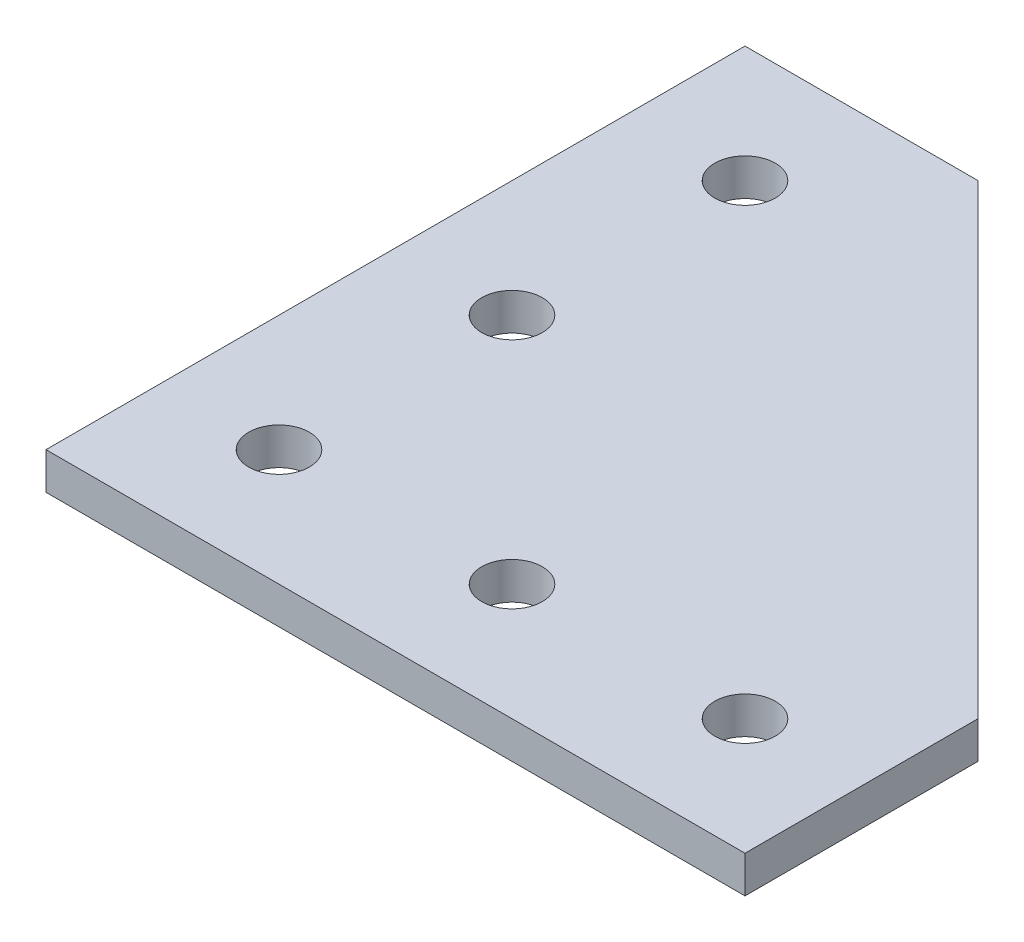
SolidWorks part; units mm, degrees
material "6061-T6 (SS)"
ref_plane "Front Plane" through (0, 0, 0) normal (0, 0, 1) x (1, 0, 0)
ref_plane "Top Plane" through (0, 0, 0) normal (0, 1, 0) x (1, 0, 0)
ref_plane "Right Plane" through (0, 0, 0) normal (1, 0, 0) x (0, 0, -1)
sketch "Sketch1" plane through (0, 0, 0) normal (0, 1, 0) x (1, 0, 0)
  line L0 (60, 0) -> (60, 20)
  line L1 (0, 0) -> (60, 0)
  line L2 (0, 0) -> (0, 60)
  line L3 (0, 60) -> (20, 60)
  line L4 (60, 20) -> (20, 60)
  line L5 (10, 10) -> (50, 10) construction
  line L6 (10, 50) -> (10, 10) construction
  circle A0 centre (50, 10) radius 2.6
  circle A1 centre (10, 50) radius 2.6
  circle A2 centre (30, 10) radius 2.6
  circle A3 centre (10, 10) radius 2.6
  circle A4 centre (10, 30) radius 2.6
  dimension "D5" = 5.2
  dimension "D1" = 60
  dimension "D3" = 20
  dimension "D6" = 40
  dimension "D7" = 10
  dimension "D8" = 10
  dimension "D9" = 40
  dimension "D2" = 60
  dimension "D4" = 20
extrude "Boss-Extrude1" add sketch "Sketch1" along normal blind 3.175
equation "\"D8@Sketch1\"=\"D7@Sketch1\""
equation "\"D9@Sketch1\"=\"D6@Sketch1\""
equation "\"D2@Sketch1\"=\"D1@Sketch1\""
equation "\"D4@Sketch1\"=\"D3@Sketch1\""
